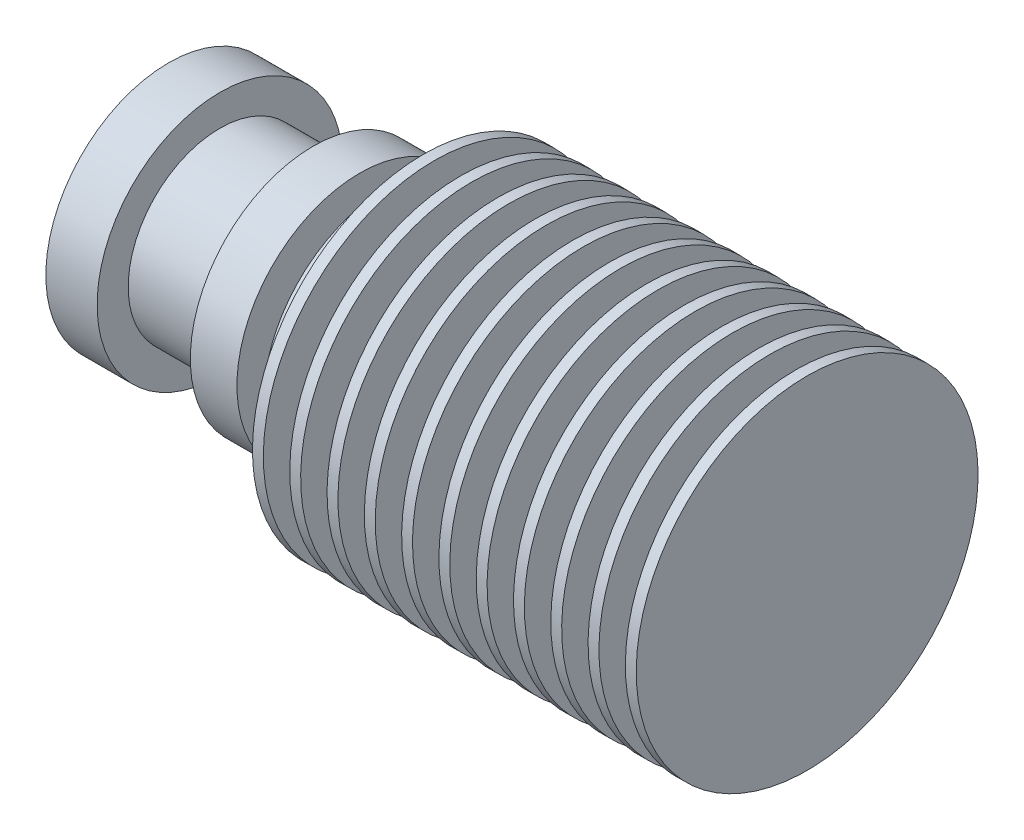
SolidWorks part; units mm, degrees
material "7075-T6 (SN)"
ref_plane "Plano frontal" through (0, 0, 0) normal (0, 0, 1) x (1, 0, 0)
ref_plane "Plano superior" through (0, 0, 0) normal (0, 1, 0) x (1, 0, 0)
ref_plane "Plano direito" through (0, 0, 0) normal (1, 0, 0) x (0, 0, -1)
sketch "Esboço1" plane through (0, 0, 0) normal (0, 0, 1) x (1, 0, 0)
  line L0 (-23.5, 7.9) -> (-23.5, 2.1) construction
  line L1 (-23.5, 5) -> (-69.1, 5) construction
  line L2 (-28, 5) -> (-28, 16)
  line L3 (-28, 16) -> (-28.7, 16)
  line L4 (-28.7, 16) -> (-28.7, 10)
  line L5 (-28.7, 10) -> (-30.4, 10)
  line L7 (-30.4, 10) -> (-30.4, 16)
  line L8 (-30.4, 16) -> (-31.1, 16)
  line L9 (-31.1, 16) -> (-31.1, 10)
  line L10 (-31.1, 10) -> (-32.8, 10)
  line L11 (-32.8, 10) -> (-32.8, 16)
  line L12 (-32.8, 16) -> (-33.5, 16)
  line L13 (-33.5, 16) -> (-33.5, 10)
  line L14 (-33.5, 10) -> (-35.2, 10)
  line L15 (-35.2, 10) -> (-35.2, 16)
  line L16 (-35.2, 16) -> (-35.9, 16)
  line L17 (-35.9, 16) -> (-35.9, 10)
  line L18 (-35.9, 10) -> (-37.6, 10)
  line L19 (-37.6, 10) -> (-37.6, 16)
  line L20 (-37.6, 16) -> (-38.3, 16)
  line L21 (-38.3, 16) -> (-38.3, 10)
  line L22 (-38.3, 10) -> (-40, 10)
  line L23 (-40, 10) -> (-40, 16)
  line L24 (-40, 16) -> (-40.7, 16)
  line L25 (-40.7, 16) -> (-40.7, 10)
  line L26 (-40.7, 10) -> (-42.4, 10)
  line L27 (-42.4, 10) -> (-42.4, 16)
  line L28 (-42.4, 16) -> (-43.1, 16)
  line L29 (-43.1, 16) -> (-43.1, 10)
  line L30 (-43.1, 10) -> (-44.8, 10)
  line L31 (-44.8, 10) -> (-44.8, 16)
  line L32 (-44.8, 16) -> (-45.5, 16)
  line L33 (-45.5, 16) -> (-45.5, 10)
  line L34 (-45.5, 10) -> (-47.2, 10)
  line L35 (-47.2, 10) -> (-47.2, 16)
  line L36 (-47.2, 16) -> (-47.9, 16)
  line L37 (-47.9, 16) -> (-47.9, 10)
  line L38 (-47.9, 10) -> (-49.6, 10)
  line L39 (-49.6, 10) -> (-49.6, 16)
  line L40 (-49.6, 16) -> (-50.3, 16)
  line L41 (-50.3, 16) -> (-50.3, 10)
  line L42 (-50.3, 10) -> (-52, 10)
  line L43 (-52, 10) -> (-52, 16)
  line L44 (-52, 16) -> (-52.7, 16)
  line L45 (-52.7, 16) -> (-52.7, 10)
  line L46 (-52.7, 10) -> (-54.4, 10)
  line L47 (-54.4, 10) -> (-54.4, 12.9)
  line L48 (-54.4, 12.9) -> (-55.1, 12.9)
  line L49 (-55.1, 12.9) -> (-55.1, 10)
  line L50 (-55.1, 10) -> (-56.8, 10)
  line L51 (-56.8, 10) -> (-56.8, 12.9)
  line L52 (-56.8, 12.9) -> (-59.8, 12.9)
  line L53 (-59.8, 12.9) -> (-59.8, 10.9)
  line L54 (-59.8, 10.9) -> (-65.8, 10.9)
  line L55 (-65.8, 10.9) -> (-65.8, 12.9)
  line L56 (-65.8, 12.9) -> (-69.1, 12.9)
  line L57 (-69.1, 12.9) -> (-69.1, 5)
  line L58 (-28, 5) -> (-69.1, 5)
  dimension "D1" = 11
  dimension "D2" = 0.7
  dimension "D3" = 1.7
  dimension "D5" = 5
  dimension "D7" = 7.9
  dimension "D8" = 3
  dimension "D9" = 6
  dimension "D10" = 3.3
  dimension "D11" = 5.9
  dimension "D6" = 11
revolve "Revolução1" add sketch "Esboço1" angle 360 about L58
